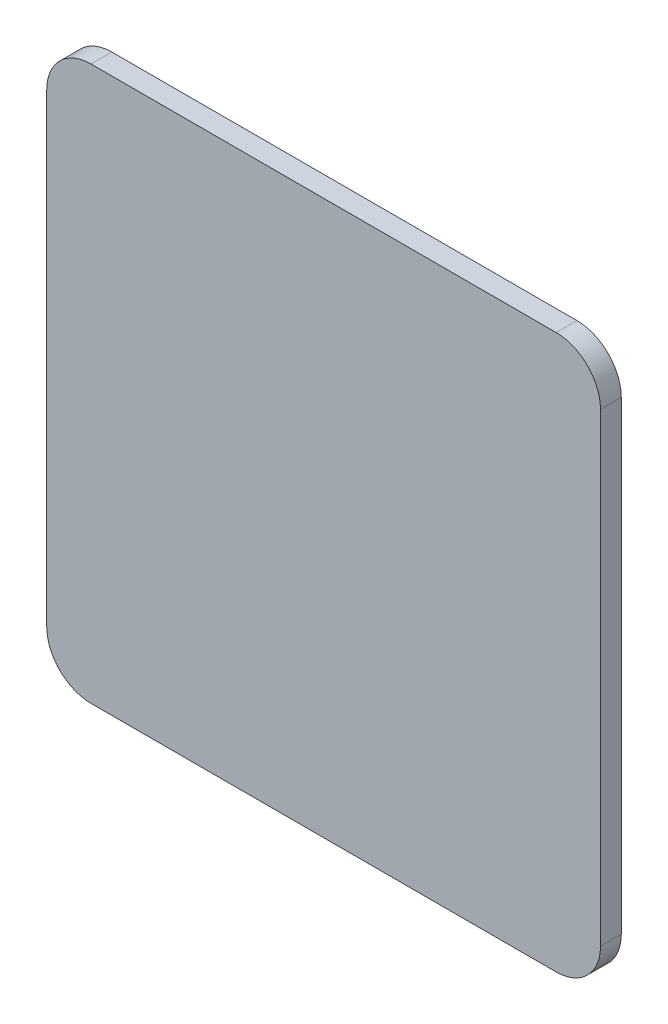
SolidWorks part; units mm, degrees
ref_plane "Front Plane" through (0, 0, 0) normal (0, 0, 1) x (1, 0, 0)
ref_plane "Top Plane" through (0, 0, 0) normal (0, 1, 0) x (1, 0, 0)
ref_plane "Right Plane" through (0, 0, 0) normal (1, 0, 0) x (0, 0, -1)
sketch "Sketch1" plane through (0, 0, 0) normal (0, 0, 1) x (1, 0, 0)
  line L0 (53.34, 58.42) -> (-53.34, 58.42)
  line L1 (53.34, 63.5) -> (-53.34, 63.5)
  line L2 (63.5, 53.34) -> (63.5, -53.34)
  line L3 (53.34, -63.5) -> (-53.34, -63.5)
  line L4 (-63.5, 53.34) -> (-63.5, -53.34)
  line L5 (63.5, 63.5) -> (-63.5, -63.5) construction
  line L6 (63.5, -63.5) -> (-63.5, 63.5) construction
  line L7 (-58.42, 53.34) -> (-58.42, -53.34)
  line L8 (53.34, -58.42) -> (-53.34, -58.42)
  line L9 (58.42, 53.34) -> (58.42, -53.34)
  arc A0 (63.5, 53.34) -> (53.34, 63.5) centre (53.34, 53.34) ccw
  arc A1 (53.34, -63.5) -> (63.5, -53.34) centre (53.34, -53.34) ccw
  arc A2 (-63.5, -53.34) -> (-53.34, -63.5) centre (-53.34, -53.34) ccw
  arc A3 (-53.34, 63.5) -> (-63.5, 53.34) centre (-53.34, 53.34) ccw
  arc A4 (-53.34, 58.42) -> (-58.42, 53.34) centre (-53.34, 53.34) ccw
  arc A5 (-58.42, -53.34) -> (-53.34, -58.42) centre (-53.34, -53.34) ccw
  arc A6 (53.34, -58.42) -> (58.42, -53.34) centre (53.34, -53.34) ccw
  arc A7 (58.42, 53.34) -> (53.34, 58.42) centre (53.34, 53.34) ccw
  point P0 (0, 0)
  dimension "D3" = 10.16
  dimension "D1" = 127
  dimension "D2" = 127
  dimension "D4" = 5.08
extrude "Boss-Extrude1" add sketch "Sketch1" along normal blind 4.7625 contours L9 A7 L0 A4 L7 A5 L8 A6 | L1 A3 L4 A2 L3 A1 L2 A0 A7 L9 A6 L8 A5 L7 A4 L0
